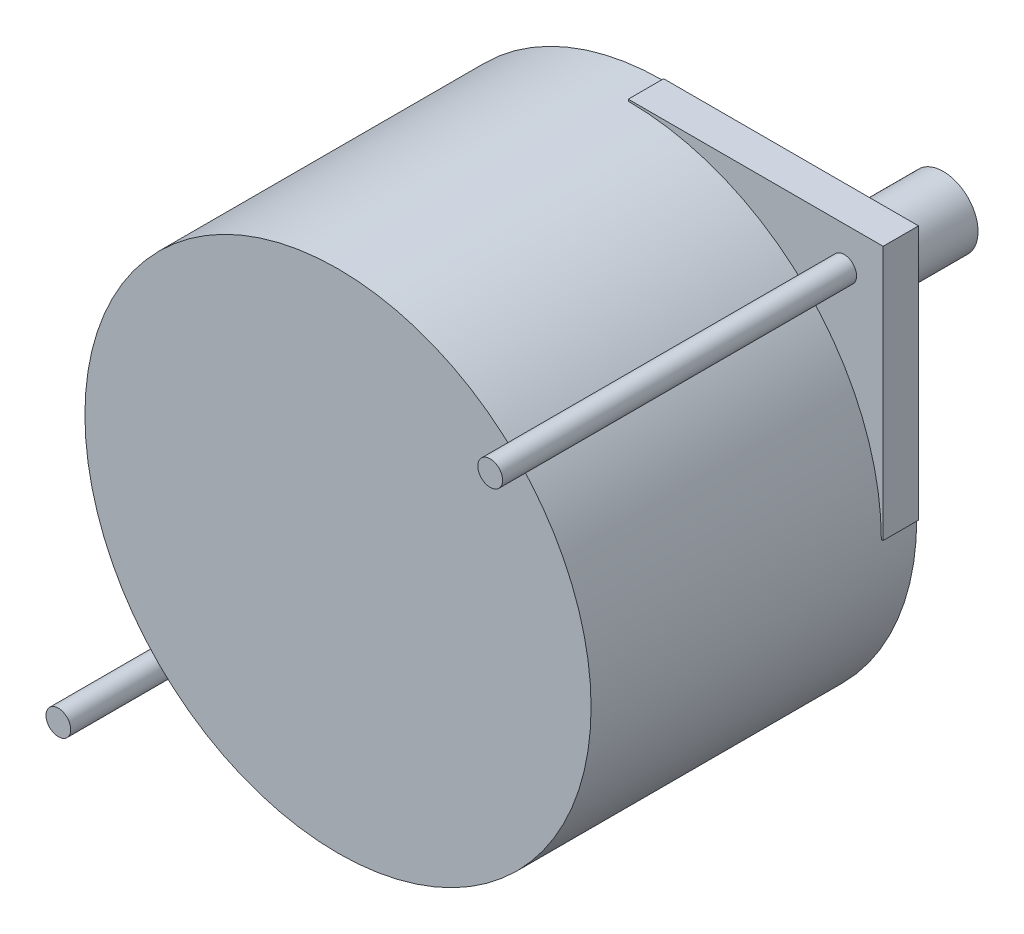
SolidWorks part; units mm, degrees
ref_plane "Front Plane" through (0, 0, 0) normal (0, 0, 1) x (1, 0, 0)
ref_plane "Top Plane" through (0, 0, 0) normal (0, 1, 0) x (1, 0, 0)
ref_plane "Right Plane" through (0, 0, 0) normal (1, 0, 0) x (0, 0, -1)
sketch "Sketch1" plane through (0, 0, 0) normal (0, 0, 1) x (1, 0, 0)
  line L1 (-0.6381, 0.9442) -> (35.9379, 0.9442)
  line L2 (-0.6381, 0.9442) -> (-0.6381, -35.6318)
  line L3 (-0.6381, -35.6318) -> (35.9379, -35.6318)
  line L4 (35.9379, 0.9442) -> (35.9379, -35.6318)
  dimension "D1" = 36.576
  dimension "D2" = 36.576
extrude "Boss-Extrude1" add sketch "Sketch1" along normal blind 2.54
sketch "Sketch2" plane through (0, 0, 2.54) normal (0, 0, 1) x (1, 0, 0)
  line L0 (35.9379, -17.3438) -> (-0.6381, -17.3438) construction
  line L1 (35.9379, -35.6318) -> (35.9379, 0.9442) construction
  line L2 (-0.6381, 0.9442) -> (-0.6381, -35.6318) construction
  line L3 (17.6499, 0.9442) -> (17.6499, -35.6318) construction
  line L6 (35.9379, 0.9442) -> (-0.6381, 0.9442) construction
  line L7 (-0.6381, -35.6318) -> (35.9379, -35.6318) construction
  line L8 (17.6499, -17.3438) -> (33.1439, -1.8498) construction
  line L9 (17.6499, -17.3438) -> (2.1559, -32.8378) construction
  circle A0 centre (33.1439, -1.8498) radius 0.889
  circle A1 centre (2.1559, -32.8378) radius 0.889
  dimension "D4" = 1.778
  dimension "D5" = 1.778
  dimension "D1" = 30.988
  dimension "D2" = 45
  dimension "D3" = 45
extrude "Boss-Extrude2" add sketch "Sketch2" along normal blind 25.4
sketch "Sketch3" plane through (0, 0, 2.54) normal (0, 0, 1) x (1, 0, 0)
  line L0 (-0.6381, 0.9442) -> (-0.6381, -17.3438)
  line L1 (-0.6381, 0.9442) -> (-0.6381, -35.6318) construction
  line L2 (-0.6381, -17.3438) -> (-0.5111, -17.3438)
  line L3 (-0.6381, 0.9442) -> (17.6499, 0.9442)
  line L4 (35.9379, 0.9442) -> (-0.6381, 0.9442) construction
  line L5 (17.6499, 0.9442) -> (17.6499, 0.8172)
  line L6 (35.9379, -35.6318) -> (17.6499, -35.6318)
  line L7 (-0.6381, -35.6318) -> (35.9379, -35.6318) construction
  line L8 (17.6499, -35.6318) -> (17.6499, -35.5048)
  line L9 (35.9379, -35.6318) -> (35.9379, -17.3438)
  line L10 (35.9379, -35.6318) -> (35.9379, 0.9442) construction
  line L11 (35.9379, -17.3438) -> (35.8109, -17.3438)
  arc A0 (17.6499, 0.8172) -> (-0.5111, -17.3438) centre (17.6499, -17.3438) ccw
  arc A1 (17.6499, -35.5048) -> (35.8109, -17.3438) centre (17.6499, -17.3438) ccw
  dimension "D1" = 36.322
extrude "Cut-Extrude4" cut sketch "Sketch3" against normal through all
sketch "Sketch4" plane through (0, 0, 0) normal (0, 0, -1) x (-1, 0, 0)
  line L0 (0.6381, -35.6318) -> (-35.9379, 0.9442) construction
  line L1 (-4.8081, -4.502) -> (-30.4917, -30.1856) construction
  arc A2 (0.5111, -17.3438) -> (-17.6499, 0.8172) centre (-17.6499, -17.3438) ccw construction
  arc A3 (-35.8109, -17.3438) -> (-17.6499, -35.5048) centre (-17.6499, -17.3438) ccw construction
  circle A4 centre (-17.6499, -17.3438) radius 8.001
  dimension "D1" = 16.002
extrude "Boss-Extrude3" add sketch "Sketch4" along normal blind 1.016
sketch "Sketch5" plane through (0, 0, -1.016) normal (0, 0, -1) x (-1, 0, 0)
  circle A0 centre (-17.6499, -17.3438) radius 2.4955
  dimension "D1" = 4.9911
extrude "Boss-Extrude4" add sketch "Sketch5" along normal blind 19.05
sketch "Sketch6" plane through (0, 0, 2.54) normal (0, 0, 1) x (1, 0, 0)
  line L0 (4.8081, -4.502) -> (30.4917, -30.1856) construction
  arc A0 (17.6499, 0.8172) -> (-0.5111, -17.3438) centre (17.6499, -17.3438) ccw construction
  arc A1 (17.6499, -35.5048) -> (35.8109, -17.3438) centre (17.6499, -17.3438) ccw construction
  circle A2 centre (17.6499, -17.3438) radius 18.161
  dimension "D1" = 36.322
extrude "Boss-Extrude5" add sketch "Sketch6" along normal blind 20.828
